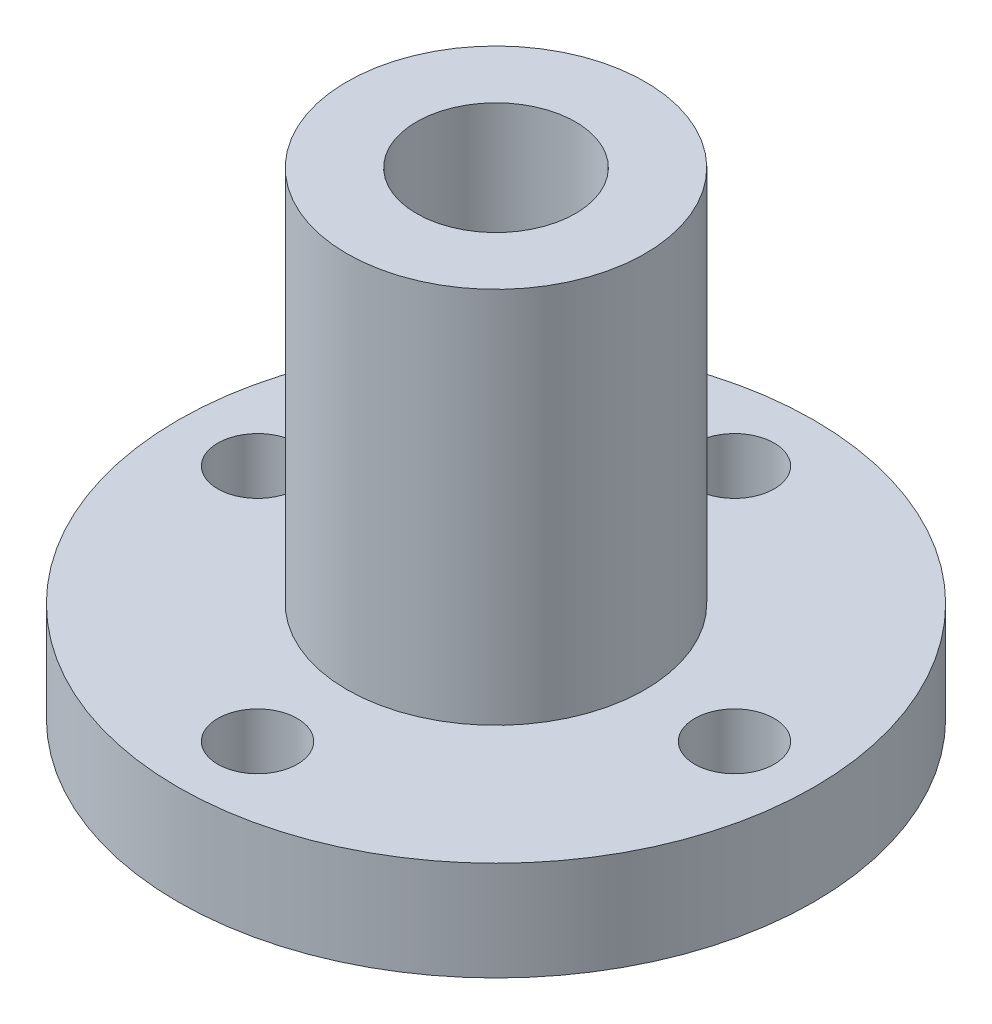
SolidWorks part; units mm, degrees
ref_plane "Front Plane" through (0, 0, 0) normal (0, 0, 1) x (1, 0, 0)
ref_plane "Top Plane" through (0, 0, 0) normal (0, 1, 0) x (1, 0, 0)
ref_plane "Right Plane" through (0, 0, 0) normal (1, 0, 0) x (0, 0, -1)
sketch "Sketch2" plane through (0, 0, 0) normal (0, 1, 0) x (1, 0, 0)
  circle A0 centre (0, 0) radius 16
  dimension "D1" = 32
extrude "Boss-Extrude1" add sketch "Sketch2" along normal blind 5
sketch "Sketch3" plane through (0, 5, 0) normal (0, 1, 0) x (1, 0, 0)
  circle A0 centre (0, 0) radius 7.5
  dimension "D1" = 15
extrude "Boss-Extrude2" add sketch "Sketch3" along normal blind 19
sketch "Sketch4" plane through (0, 24, 0) normal (0, 1, 0) x (1, 0, 0)
  circle A0 centre (0, 0) radius 4
  dimension "D1" = 8
extrude "Cut-Extrude1" cut sketch "Sketch4" against normal blind 50
sketch "Sketch5" plane through (0, 5, 0) normal (0, 1, 0) x (1, 0, 0)
  circle A0 centre (0, 12) radius 2
  circle A1 centre (0, -12) radius 2
  circle A2 centre (-12, 0) radius 2
  circle A3 centre (12, 0) radius 2
  dimension "D1" = 4
  dimension "D2" = 4
  dimension "D5" = 4
  dimension "D6" = 4
  dimension "D3" = 24
  dimension "D4" = 12
  dimension "D7" = 24
  dimension "D8" = 12
extrude "Cut-Extrude2" cut sketch "Sketch5" against normal blind 50
